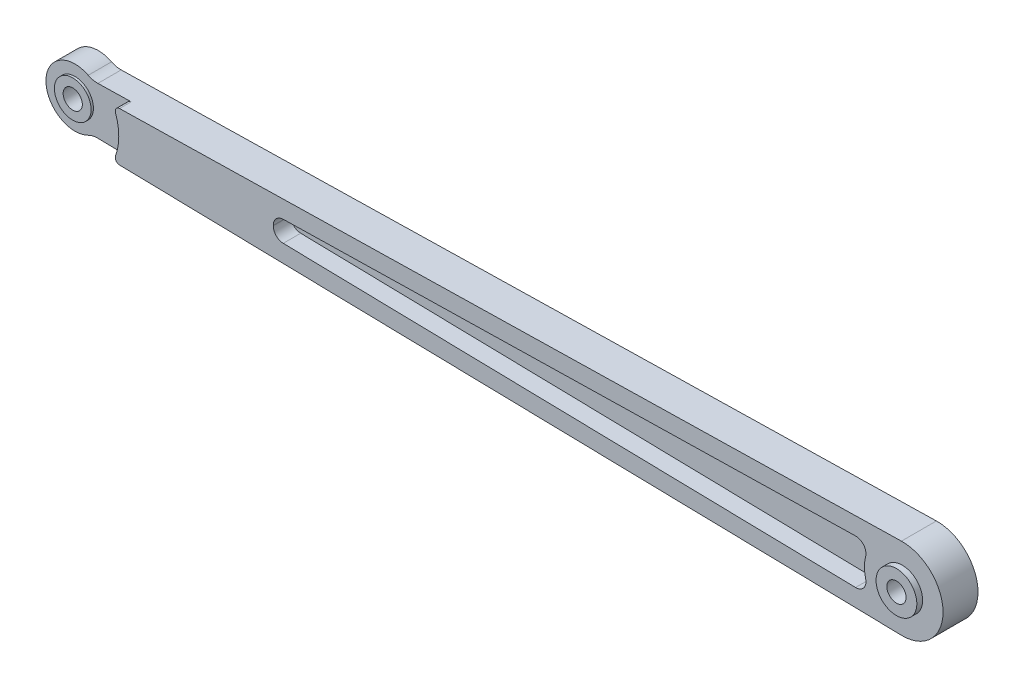
SolidWorks part; units mm, degrees
material "6061-T6 (SS)"
ref_plane "Front Plane" through (0, 0, 0) normal (0, 0, 1) x (1, 0, 0)
ref_plane "Top Plane" through (0, 0, 0) normal (0, 1, 0) x (1, 0, 0)
ref_plane "Right Plane" through (0, 0, 0) normal (1, 0, 0) x (0, 0, -1)
sketch "Sketch1" plane through (0, 0, 0) normal (0, 0, 1) x (1, 0, 0)
  line L0 (-0.1458, 6.9985) -> (-144.0833, 3.9991)
  line L1 (-0.1458, -6.9985) -> (-144.0833, -3.9991)
  circle A0 centre (-144, 0) radius 1.65
  circle A1 centre (0, 0) radius 7
  circle A2 centre (-144, 0) radius 4
  circle A3 centre (-144, 0) radius 5
  point P6 (-140, 0)
  dimension "D1" = 3.3
  dimension "D2" = 14
  dimension "D4" = 8
  dimension "D5" = 10
  dimension "D3" = 140
extrude "Boss-Extrude1" add sketch "Sketch1" along normal blind 6 contours A2 A0 | A2 L1 A1 L0 | A1 | L0 A3 L1 A2 | L1 A3 L0 A2
sketch "Sketch2" plane through (0, 0, 6) normal (0, 0, 1) x (1, 0, 0)
  circle A1 centre (0, 0) radius 3.5
  dimension "D1" = 7
extrude "Boss-Extrude2" add sketch "Sketch2" along normal blind 1
sketch "Sketch4" plane through (0, 0, 7) normal (0, 0, 1) x (1, 0, 0)
  circle A0 centre (0, 0) radius 1.65
  dimension "D1" = 3.3
extrude "Cut-Extrude1" cut sketch "Sketch4" against normal blind 12
sketch "Sketch7" plane through (0, 0, 6) normal (0, 0, 1) x (1, 0, 0)
  circle A0 centre (-144, 0) radius 9.5
  dimension "D1" = 19
extrude "Cut-Extrude3" cut sketch "Sketch7" against normal blind 2
fillet "Fillet2" radius 0.75 2 edges at (-135.4684, 4.1786, 5) (-135.4684, -4.1786, 5)
fillet "Fillet3" radius 3.5 2 edges at (-141.084, 4.0616, 2) (-141.084, -4.0616, 2)
sketch "Sketch8" plane through (0, 0, 4) normal (0, 0, 1) x (1, 0, 0)
  circle A0 centre (-144, 0) radius 1.65
  circle A1 centre (-144, 0) radius 3.15
  circle A2 centre (-144, 0) radius 1.65 construction
  dimension "D1" = 1.5
extrude "Boss-Extrude5" add sketch "Sketch8" along normal blind 0.4
sketch "Sketch9" plane through (0, 0, 6) normal (0, 0, 1) x (1, 0, 0)
  line L0 (-8.0189, -3.8338) -> (-106.2622, -1.7866)
  line L1 (-8.0189, 3.8338) -> (-106.2622, 1.7866)
  line L2 (-0.1458, 6.9985) -> (-134.3643, 4.2017) construction
  line L3 (-0.1458, -6.9985) -> (-134.3643, -4.2017) construction
  arc A0 (-6.2892, -1.6421) -> (-6.2892, 1.6421) centre (0, 0) cw
  arc A1 (-107.9757, -0.0353) -> (-107.9757, 0.0353) centre (-144, 0) ccw
  circle A2 centre (0, 0) radius 3.5 construction
  arc A3 (-106.2622, 1.7866) -> (-107.9757, 0.0353) centre (-106.2257, 0.037) ccw
  arc A4 (-107.9757, -0.0353) -> (-106.2622, -1.7866) centre (-106.2257, -0.037) ccw
  arc A5 (-8.0189, -3.8338) -> (-6.2892, -1.6421) centre (-7.9824, -2.0842) ccw
  arc A6 (-6.2892, 1.6421) -> (-8.0189, 3.8338) centre (-7.9824, 2.0842) ccw
  point P16 (-108.0182, 1.75)
  point P19 (-108.0182, -1.75)
  dimension "D3" = 3.5
  dimension "D4" = 3
  dimension "D5" = 1.75
  dimension "D1" = 3
  dimension "D2" = 3
extrude "Cut-Extrude4" cut sketch "Sketch9" against normal blind 3
